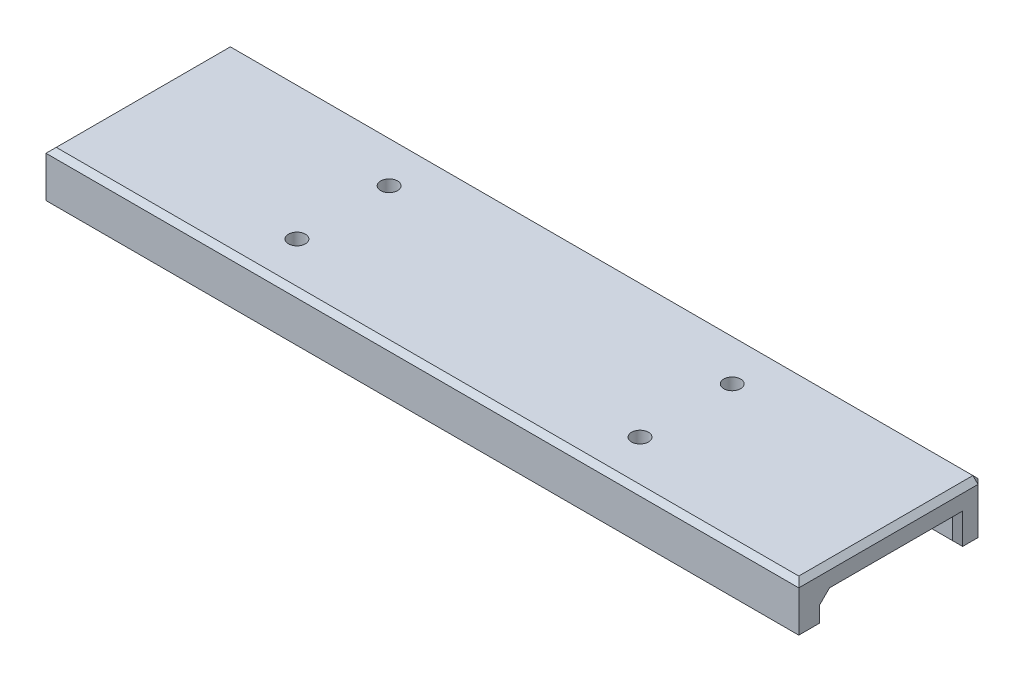
SolidWorks part; units mm, degrees
material "ABS"
ref_plane "Front Plane" through (0, 0, 0) normal (0, 0, 1) x (1, 0, 0)
ref_plane "Top Plane" through (0, 0, 0) normal (0, 1, 0) x (1, 0, 0)
ref_plane "Right Plane" through (0, 0, 0) normal (1, 0, 0) x (0, 0, -1)
sketch "Sketch1" plane through (0, 0, 0) normal (0, 1, 0) x (1, 0, 0)
  line L1 (-73.5, -18) -> (73.5, -18)
  line L2 (-73.5, -18) -> (-73.5, 18)
  line L3 (-73.5, 18) -> (73.5, 18)
  line L4 (73.5, -18) -> (73.5, 18)
  line L5 (-73.5, -18) -> (73.5, 18) construction
  line L6 (-73.5, 18) -> (73.5, -18) construction
  point P0 (0, 0)
  dimension "D1" = 147
  dimension "D2" = 36
extrude "Boss-Extrude1" add sketch "Sketch1" along normal mid plane 10
sketch "Sketch2" plane through (0, 0, 0) normal (1, 0, 0) x (0, 0, -1)
  line L0 (-13, 0) -> (13, 0)
  line L1 (13, 0) -> (13, -5)
  line L2 (-18, -5) -> (18, -5) construction
  line L3 (-13, -5) -> (-13, 0)
  line L4 (-18, 5) -> (-18, -5) construction
  line L5 (-13, -5) -> (13, -5)
  dimension "D1" = 5
extrude "Cut-Extrude1" cut sketch "Sketch2" against normal through all both and the other way through all
chamfer "Chamfer1" distance 1 angle 45 19 edges at (73.5, -2.5, 13) (0, -5, 18) (0, 0, 13) (73.5, 0, 0) (73.5, -2.5, -13) (0, -5, -13) (-73.5, -2.5, -13) (-73.5, 0, 0) (-73.5, -2.5, 13) (-73.5, -5, 15.5) (0, -5, 13) (73.5, -5, 15.5) (0, 5, 18) (-73.5, 5, 0) (73.5, 5, 0) (0, 5, -18) (73.5, 0, -18) (0, -5, -18) (-73.5, 0, -18)
hole_wizard "Tap Drill for M4x0.7 Tap1" positions "Sketch3" profile "Sketch4" hole size "M4x0.7" standard "ANSI Metric"
sketch "Sketch3" plane through (-88.5, 5, -18) normal (0, 1, 0) x (-1, 0, 0)
  point P0 (-55, 27)
  point P3 (-122, 27)
  point P6 (-55, 9)
  point P9 (-122, 9)
sketch "Sketch4" plane through (-33.5, 5, 9) normal (1, 0, 0) x (0, 0, 1)
  line L0 (0, 0) -> (0, 14.9914)
  line L1 (0, 14.9914) -> (1.65, 14)
  line L2 (1.65, 14) -> (1.65, 0)
  line L3 (1.65, 0) -> (0, 0)
  line L4 (0, 14.9914) -> (-1.65, 14) construction
  line L5 (0, -6.35) -> (0, 107.95) construction
  dimension "Hole Dia." = 3.3
  dimension "Hole Depth" = 14
  dimension "Drill Angle" = 118
